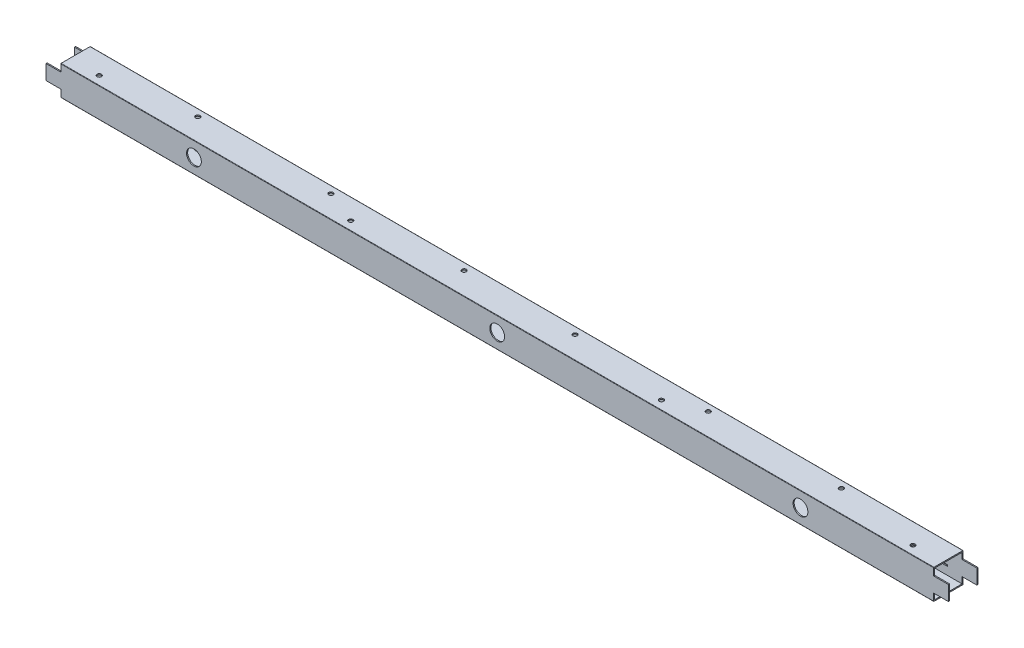
SolidWorks part; units mm, degrees
ref_plane "Front Plane" through (0, 0, 0) normal (0, 0, 1) x (1, 0, 0)
ref_plane "Top Plane" through (0, 0, 0) normal (0, 1, 0) x (1, 0, 0)
ref_plane "Right Plane" through (0, 0, 0) normal (1, 0, 0) x (0, 0, -1)
sketch "Sketch2" plane through (0, 0, 0) normal (1, 0, 0) x (0, 0, -1)
  line L0 (1.5, 1.5) -> (38.5, 1.5)
  line L1 (0.5, 0) -> (39.5, 0)
  line L2 (0, 0.5) -> (0, 39.5)
  line L3 (0.5, 40) -> (39.5, 40)
  line L4 (40, 0.5) -> (40, 39.5)
  line L5 (38.5, 1.5) -> (38.5, 38.5)
  line L6 (1.5, 38.5) -> (38.5, 38.5)
  line L7 (1.5, 1.5) -> (1.5, 38.5)
  arc A0 (39.5, 0) -> (40, 0.5) centre (39.5, 0.5) ccw
  arc A1 (0.5, 0) -> (0, 0.5) centre (0.5, 0.5) cw
  arc A2 (0, 39.5) -> (0.5, 40) centre (0.5, 39.5) cw
  arc A3 (39.5, 40) -> (40, 39.5) centre (39.5, 39.5) cw
  arc A4 (38.5, 1.5) -> (38.5, 1.5) centre (38.5, 1.5) ccw
  arc A5 (38.5, 38.5) -> (38.5, 38.5) centre (38.5, 38.5) cw
  arc A6 (1.5, 38.5) -> (1.5, 38.5) centre (1.5, 38.5) cw
  arc A7 (1.5, 1.5) -> (1.5, 1.5) centre (1.5, 1.5) cw
  point P9 (0, 0)
  dimension "D3" = 0.5
  dimension "D1" = 40
  dimension "D2" = 40
  dimension "D4" = 1.5
extrude "Boss-Extrude1" add sketch "Sketch2" along normal blind 1220
sketch "Sketch3" plane through (0, 0, -40) normal (0, 0, -1) x (-1, 0, 0)
  line L0 (-1220, 20) -> (-1140, 20) construction
  line L1 (-1220, 40) -> (-1200, 40)
  line L2 (-1220, 40) -> (-1220, 30)
  line L3 (-1220, 30) -> (-1200, 30)
  line L4 (-1200, 40) -> (-1200, 30)
  line L5 (-1220, 0.5) -> (-1220, 39.5) construction
  line L6 (-1200, 0) -> (-1200, 10)
  line L7 (-1220, 10) -> (-1200, 10)
  line L8 (-1220, 0) -> (-1220, 10)
  line L9 (-1220, 0) -> (-1200, 0)
  line L10 (-610, 39.5) -> (-610, 0.5) construction
  line L11 (-1220, 39.5) -> (0, 39.5) construction
  line L12 (-1220, 0.5) -> (0, 0.5) construction
  line L13 (0, 0) -> (-20, 0)
  line L14 (0, 0) -> (0, 10)
  line L15 (0, 10) -> (-20, 10)
  line L16 (-20, 0) -> (-20, 10)
  line L17 (-20, 40) -> (-20, 30)
  line L18 (0, 30) -> (-20, 30)
  line L19 (0, 40) -> (0, 30)
  line L20 (0, 40) -> (-20, 40)
  dimension "D1" = 10
  dimension "D2" = 20
extrude "Cut-Extrude1" cut sketch "Sketch3" against normal blind 50
sketch "Sketch4" plane through (0, 0, -40) normal (0, 0, -1) x (-1, 0, 0)
  line L1 (-40, 14) -> (-120, 14)
  line L2 (-40, 14) -> (-40, 12)
  line L3 (-40, 12) -> (-120, 12)
  line L4 (-120, 14) -> (-120, 12)
  line L5 (-133, 12) -> (-135, 12)
  line L6 (-133, 12) -> (-133, 6)
  line L7 (-133, 6) -> (-135, 6)
  line L8 (-135, 12) -> (-135, 6)
  line L11 (-20, 10) -> (-20, 0.5) construction
  line L12 (-1200, 0) -> (-20, 0) construction
  line L13 (-610, 39.5) -> (-610, 0.5) construction
  line L14 (-1200, 39.5) -> (-20, 39.5) construction
  line L15 (-1200, 0.5) -> (-20, 0.5) construction
  line L16 (-1085, 12) -> (-1085, 6)
  line L17 (-1087, 6) -> (-1085, 6)
  line L18 (-1087, 12) -> (-1087, 6)
  line L19 (-1087, 12) -> (-1085, 12)
  line L20 (-1100, 14) -> (-1100, 12)
  line L21 (-1180, 12) -> (-1100, 12)
  line L22 (-1180, 14) -> (-1180, 12)
  line L23 (-1180, 14) -> (-1100, 14)
  dimension "D1" = 20
  dimension "D2" = 12
  dimension "D3" = 2
  dimension "D4" = 80
  dimension "D5" = 2
  dimension "D6" = 6
extrude "Cut-Extrude2" cut sketch "Sketch4" against normal blind 20
sketch "Sketch5" plane through (0, 0, -40) normal (0, 0, -1) x (-1, 0, 0)
  line L0 (-1220, 10) -> (-1220, 30) construction
  line L1 (-610, 0.5) -> (-610, 39.5) construction
  line L2 (-1200, 0.5) -> (-20, 0.5) construction
  line L3 (-1200, 39.5) -> (-20, 39.5) construction
  circle A0 centre (-1020, 20) radius 10
  circle A1 centre (-610, 20) radius 10
  circle A2 centre (-200, 20) radius 10
  point P5 (-1220, 20)
  dimension "D1" = 200
  dimension "D2" = 20
extrude "Cut-Extrude3" cut sketch "Sketch5" against normal through all and the other way through all
sketch "Sketch6" plane through (0, 0, 0) normal (0, -1, 0) x (1, 0, 0)
  line L0 (610, -0.5) -> (610, -39.5) construction
  line L1 (1200, -0.5) -> (20, -0.5) construction
  line L2 (1200, -39.5) -> (20, -39.5) construction
  line L3 (1200, -0.5) -> (1200, -39.5) construction
  line L4 (1200, 0) -> (20, 0) construction
  circle A0 centre (1160, -12) radius 3
  circle A1 centre (820, -12) radius 3
  circle A2 centre (400, -12) radius 3
  circle A3 centre (60, -12) radius 3
  point P10 (0, 0)
  point P11 (0, 0)
  dimension "D1" = 6
  dimension "D3" = 340
  dimension "D2" = 40
  dimension "D4" = 12
extrude "Cut-Extrude4" cut sketch "Sketch6" against normal through all
sketch "Sketch7" plane through (0, 0, 0) normal (0, -1, 0) x (1, 0, 0)
  line L0 (1200, -0.5) -> (1200, -39.5) construction
  line L1 (1200, -40) -> (20, -40) construction
  line L2 (610, -39.5) -> (610, -0.5) construction
  line L3 (1200, -39.5) -> (20, -39.5) construction
  line L4 (1200, -0.5) -> (20, -0.5) construction
  circle A0 centre (1045, -30.25) radius 3
  circle A1 centre (865, -30.25) radius 3
  circle A2 centre (685, -30.25) radius 3
  circle A3 centre (535, -30.25) radius 3
  circle A4 centre (355, -30.25) radius 3
  circle A5 centre (175, -30.25) radius 3
  dimension "D1" = 155
  dimension "D2" = 6
  dimension "D3" = 9.75
  dimension "D4" = 3
extrude "Cut-Extrude5" cut sketch "Sketch7" against normal through all
